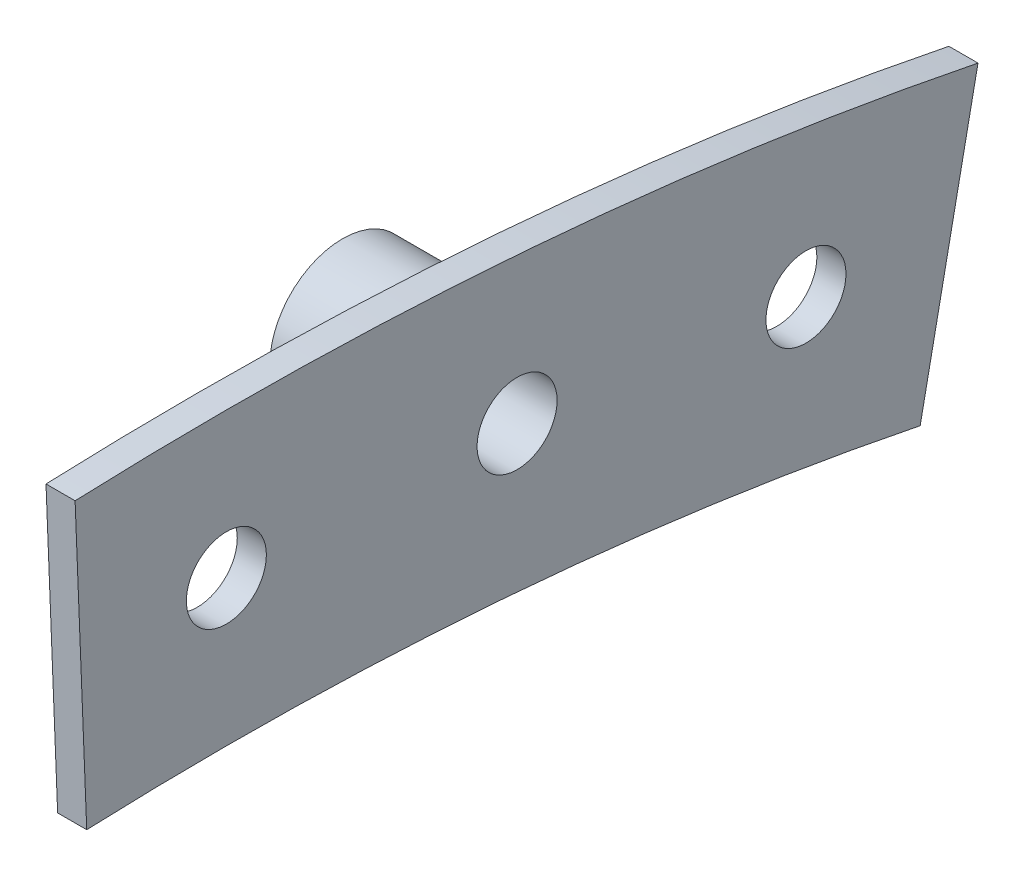
SolidWorks part; units mm, degrees
ref_plane "Front Plane" through (0, 0, 0) normal (0, 0, 1) x (1, 0, 0)
ref_plane "Top Plane" through (0, 0, 0) normal (0, 1, 0) x (1, 0, 0)
ref_plane "Right Plane" through (0, 0, 0) normal (1, 0, 0) x (0, 0, -1)
sketch "Sketch1" plane through (0, 0, 0) normal (1, 0, 0) x (0, 0, -1)
  line L0 (-12.1896, 304.5562) -> (-13.2054, 329.9358)
  line L1 (0, 317.5) -> (0, 0) construction
  line L2 (60.568, 298.7215) -> (65.6153, 323.615)
  line L3 (65.6153, 323.615) -> (0, 0) construction
  arc A0 (0, 317.5) -> (50.5969, 313.4425) centre (0, 0) cw
  circle A1 centre (0, 317.5) radius 3.4925
  circle A2 centre (25.3797, 316.484) radius 3.4925
  circle A3 centre (50.5969, 313.4425) radius 3.4925
  arc A4 (-12.1896, 304.5562) -> (60.568, 298.7215) centre (0, 0) cw
  arc A5 (-13.2054, 329.9358) -> (65.6153, 323.615) centre (0, 0) cw
  point P5 (25.3797, 316.484)
  point P13 (-12.6975, 317.246)
  point P15 (63.0916, 311.1683)
  dimension "D1" = 317.5
  dimension "D3" = 6.985
  dimension "D4" = 6.985
  dimension "D5" = 6.985
  dimension "D6" = 304.8
  dimension "D7" = 25.4
  dimension "D8" = 12.6975
  dimension "D2" = 25.4
  dimension "D9" = 12.7
extrude "Boss-Extrude1" add sketch "Sketch1" along normal blind 2.54
sketch "Sketch2" plane through (0, 0, 0) normal (-1, 0, 0) x (0, 0, 1)
  circle A0 centre (-25.3797, 316.484) radius 6.35
  dimension "D1" = 12.7
extrude "Boss-Extrude2" add sketch "Sketch2" along normal blind 12.7 contours A0
sketch "Sketch4" plane through (0, 0, 0) normal (1, 0, 0) x (0, 0, -1)
  circle A0 centre (25.3797, 316.484) radius 3.4925
  dimension "D1" = 6.985
extrude "Cut-Extrude1" cut sketch "Sketch4" against normal blind 6.35
